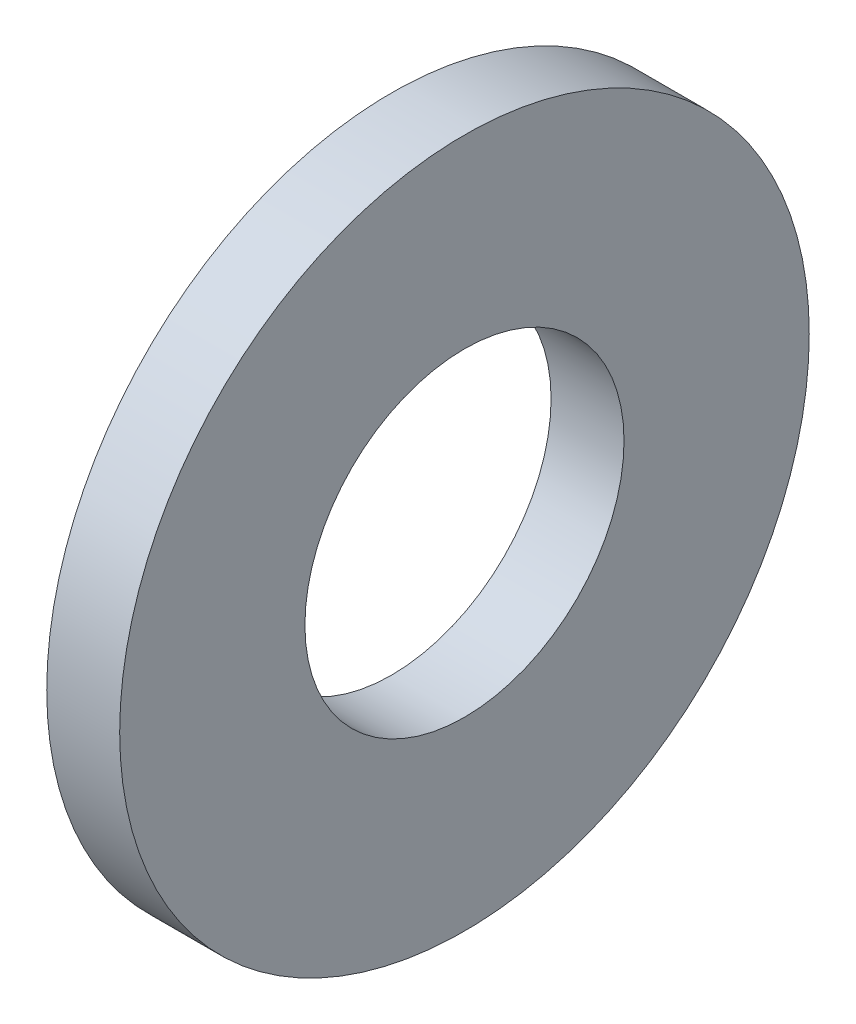
SolidWorks part; units mm, degrees
ref_plane "Front Plane" through (0, 0, 0) normal (0, 0, 1) x (1, 0, 0)
ref_plane "Top Plane" through (0, 0, 0) normal (0, 1, 0) x (1, 0, 0)
ref_plane "Right Plane" through (0, 0, 0) normal (1, 0, 0) x (0, 0, -1)
sketch "Sketch1" plane through (0, 0, 0) normal (1, 0, 0) x (0, 0, -1)
  circle A0 centre (0, 0) radius 13
  circle A1 centre (0, 0) radius 6 construction
  circle A2 centre (0, 0) radius 6.016
  dimension "OD" = 26
  dimension "For Shaft Diameter" = 12
  dimension "ID" = 12.032
sketch "Sketch2" plane through (0, 0, 0) normal (0, 0, 1) x (1, 0, 0)
  line L0 (1.375, 0) -> (-1.375, 0) construction
  line L1 (1.375, -13) -> (-1.375, -13) construction
  line L2 (1.375, -13) -> (1.375, 13) construction
  line L3 (1.375, 13) -> (-1.375, 13) construction
  line L4 (-1.375, -13) -> (-1.375, 13) construction
  point P6 (0, 13)
  point P9 (0, -13)
  dimension "Thickness" = 2.75
sketch "Sketch3" plane through (0, 0, 0) normal (1, 0, 0) x (0, 0, -1)
  circle A1 centre (0, 0) radius 13 construction
  circle A3 centre (0, 0) radius 13
  circle A4 centre (0, 0) radius 6.016 construction
  circle A5 centre (0, 0) radius 6.016
extrude "Boss-Extrude1" add sketch "Sketch3" along normal up to vertex (1.375 mm away) and the other way up to vertex (1.375 mm away) up to point (1.375, 13, 0) other way up to point (-1.375, 13, 0)
